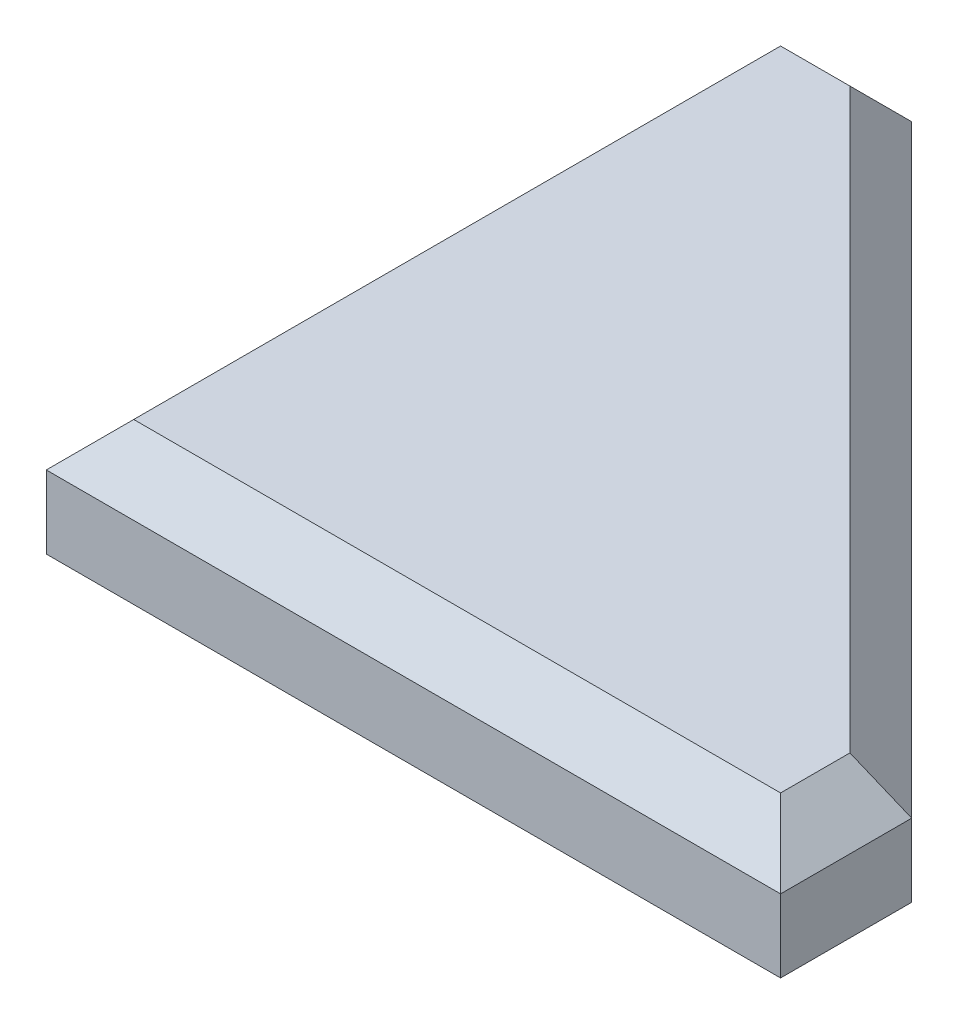
SolidWorks part; units mm, degrees
ref_plane "Plan de face" through (0, 0, 0) normal (0, 0, 1) x (1, 0, 0)
ref_plane "Plan de dessus" through (0, 0, 0) normal (0, 1, 0) x (1, 0, 0)
ref_plane "Plan de droite" through (0, 0, 0) normal (1, 0, 0) x (0, 0, -1)
sketch "Esquisse1" plane through (0, 0, 0) normal (0, 1, 0) x (1, 0, 0)
  line L0 (0, 0) -> (0, 50.397)
  line L1 (0, 50.397) -> (9, 50.397)
  line L2 (9, 50.397) -> (50.397, 9)
  line L3 (50.397, 9) -> (50.397, 0)
  line L4 (50.397, 0) -> (0, 0)
  dimension "D1" = 42
  dimension "D2" = 9
extrude "Boss.-Extru.1" add sketch "Esquisse1" along normal blind 8
chamfer "Chanfrein1" distance 3 angle 45 5 edges at (25.1985, 8, 0) (50.397, 8, -4.5) (29.6985, 8, -29.6985) (4.5, 8, -50.397) (0, 8, -25.1985)
